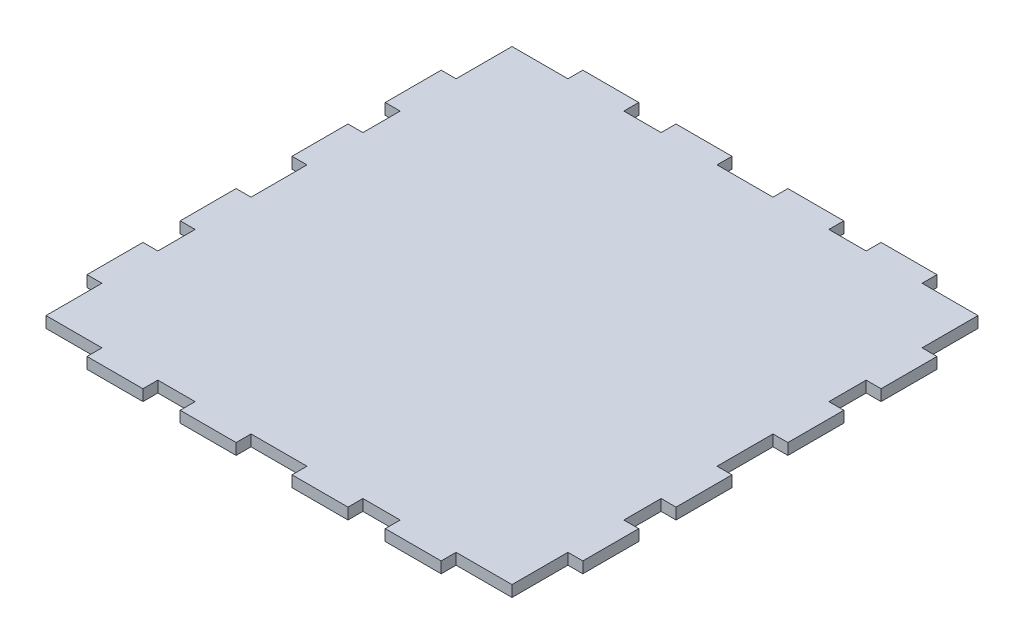
SolidWorks part; units mm, degrees
material "Oak"
ref_plane "Front Plane" through (0, 0, 0) normal (0, 0, 1) x (1, 0, 0)
ref_plane "Top Plane" through (0, 0, 0) normal (0, 1, 0) x (1, 0, 0)
ref_plane "Right Plane" through (0, 0, 0) normal (1, 0, 0) x (0, 0, -1)
sketch "Sketch1" plane through (0, 0, 0) normal (0, 1, 0) x (1, 0, 0)
  line L0 (-1.5, 0) -> (-62.5, 0) construction
  line L6 (7.5, -66.5) -> (7.5, -62.5)
  line L11 (-7.5, -62.5) -> (7.5, -62.5)
  line L12 (-7.5, -66.5) -> (-7.5, -62.5)
  line L14 (7.5, -66.5) -> (22.5, -66.5)
  line L15 (62.5, -59) -> (62.5, -62.5)
  line L31 (57.5, -62.5) -> (47.5, -62.5)
  line L32 (47.5, -62.5) -> (47.5, -66.5)
  line L33 (32.5, -62.5) -> (22.5, -62.5)
  line L34 (22.5, -62.5) -> (22.5, -66.5)
  line L35 (-22.5, -62.5) -> (-22.5, -66.5)
  line L36 (-32.5, -62.5) -> (-22.5, -62.5)
  line L37 (-32.5, -62.5) -> (-32.5, -66.5)
  line L39 (-47.5, -62.5) -> (-47.5, -66.5)
  line L40 (-59, -62.5) -> (-47.5, -62.5)
  line L41 (-22.5, -66.5) -> (-7.5, -66.5)
  line L42 (-47.5, -66.5) -> (-32.5, -66.5)
  line L44 (32.5, -62.5) -> (32.5, -66.5)
  line L45 (32.5, -66.5) -> (47.5, -66.5)
  line L61 (62.5, -47.5) -> (62.5, -59)
  line L62 (66.5, -47.5) -> (62.5, -47.5)
  line L63 (62.5, -22.5) -> (62.5, -32.5)
  line L64 (62.5, -32.5) -> (66.5, -32.5)
  line L65 (66.5, -22.5) -> (62.5, -22.5)
  line L69 (-62.5, -47.5) -> (-62.5, -59)
  line L70 (-66.5, -47.5) -> (-62.5, -47.5)
  line L71 (-62.5, -32.5) -> (-66.5, -32.5)
  line L72 (-62.5, -22.5) -> (-62.5, -32.5)
  line L73 (-66.5, -22.5) -> (-62.5, -22.5)
  line L85 (66.5, -32.5) -> (66.5, -47.5)
  line L87 (62.5, -62.5) -> (57.5, -62.5)
  line L92 (-62.5, -59) -> (-62.5, -62.5)
  line L93 (-62.5, -62.5) -> (-59, -62.5)
  line L96 (-66.5, -32.5) -> (-66.5, -47.5)
  line L101 (66.5, -22.5) -> (66.5, -7.5)
  line L102 (-66.5, -22.5) -> (-66.5, -7.5)
  line L103 (66.5, -7.5) -> (62.5, -7.5)
  line L104 (62.5, -7.5) -> (62.5, 7.5)
  line L105 (-66.5, -7.5) -> (-62.5, -7.5)
  line L106 (-62.5, -7.5) -> (-62.5, 7.5)
  line L107 (-66.5, 7.5) -> (-62.5, 7.5)
  line L108 (66.5, 7.5) -> (62.5, 7.5)
  line L109 (-66.5, 22.5) -> (-66.5, 7.5)
  line L110 (66.5, 22.5) -> (66.5, 7.5)
  line L111 (-66.5, 32.5) -> (-66.5, 47.5)
  line L112 (-62.5, 62.5) -> (-59, 62.5)
  line L113 (-62.5, 59) -> (-62.5, 62.5)
  line L114 (62.5, 62.5) -> (57.5, 62.5)
  line L115 (66.5, 32.5) -> (66.5, 47.5)
  line L116 (-66.5, 22.5) -> (-62.5, 22.5)
  line L117 (-62.5, 22.5) -> (-62.5, 32.5)
  line L118 (-62.5, 32.5) -> (-66.5, 32.5)
  line L119 (-66.5, 47.5) -> (-62.5, 47.5)
  line L120 (-62.5, 47.5) -> (-62.5, 59)
  line L121 (66.5, 22.5) -> (62.5, 22.5)
  line L122 (62.5, 32.5) -> (66.5, 32.5)
  line L123 (62.5, 22.5) -> (62.5, 32.5)
  line L124 (66.5, 47.5) -> (62.5, 47.5)
  line L125 (62.5, 47.5) -> (62.5, 59)
  line L126 (32.5, 66.5) -> (47.5, 66.5)
  line L127 (32.5, 62.5) -> (32.5, 66.5)
  line L128 (-47.5, 66.5) -> (-32.5, 66.5)
  line L129 (-22.5, 66.5) -> (-7.5, 66.5)
  line L130 (-59, 62.5) -> (-47.5, 62.5)
  line L131 (-47.5, 62.5) -> (-47.5, 66.5)
  line L132 (-32.5, 62.5) -> (-32.5, 66.5)
  line L133 (-32.5, 62.5) -> (-22.5, 62.5)
  line L134 (-22.5, 62.5) -> (-22.5, 66.5)
  line L135 (22.5, 62.5) -> (22.5, 66.5)
  line L136 (32.5, 62.5) -> (22.5, 62.5)
  line L137 (47.5, 62.5) -> (47.5, 66.5)
  line L138 (57.5, 62.5) -> (47.5, 62.5)
  line L139 (62.5, 59) -> (62.5, 62.5)
  line L140 (7.5, 66.5) -> (22.5, 66.5)
  line L141 (-7.5, 66.5) -> (-7.5, 62.5)
  line L142 (-7.5, 62.5) -> (7.5, 62.5)
  line L143 (7.5, 66.5) -> (7.5, 62.5)
  point P11 (-47.5, -64.5)
  point P12 (-62.5, 0)
  point P18 (62.5, 0)
  dimension "D4" = 10
  dimension "D5" = 15
  dimension "D6" = 15
  dimension "D7" = 15
  dimension "D8" = 15
  dimension "D9" = 15
  dimension "D10" = 15
  dimension "D11" = 15
  dimension "D12" = 62.5
  dimension "D13" = 10
  dimension "D14" = 7.5
  dimension "D15" = 62.5
  dimension "D16" = 62.5
  dimension "D17" = 15
  dimension "D26" = 15
  dimension "D27" = 15
  dimension "D28" = 15
  dimension "D30" = 10
extrude "Boss-Extrude1" add sketch "Sketch1" along normal blind 3
